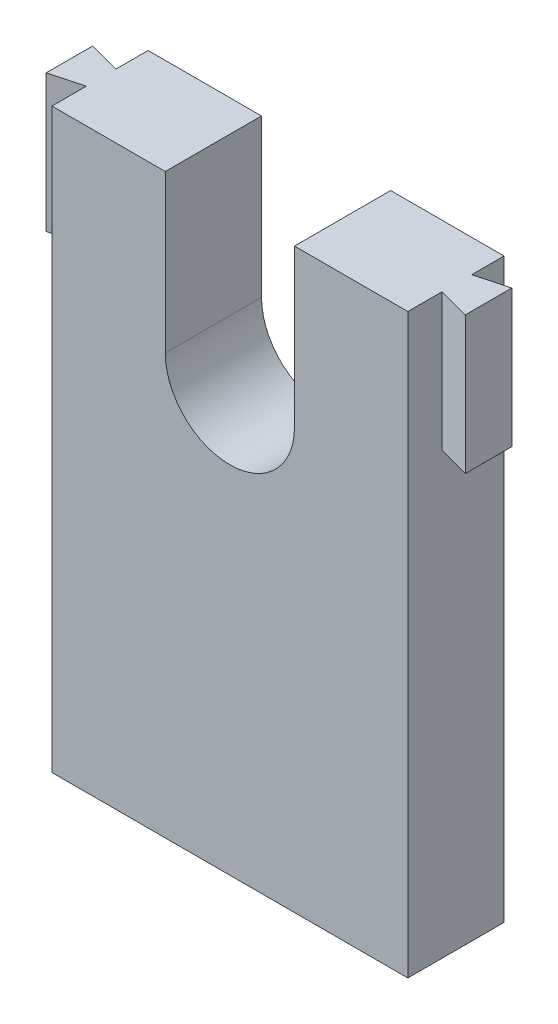
SolidWorks part; units mm, degrees
ref_plane "Front Plane" through (0, 0, 0) normal (0, 0, 1) x (1, 0, 0)
ref_plane "Top Plane" through (0, 0, 0) normal (0, 1, 0) x (1, 0, 0)
ref_plane "Right Plane" through (0, 0, 0) normal (1, 0, 0) x (0, 0, -1)
sketch "Sketch1" plane through (0, 0, 0) normal (0, 0, 1) x (1, 0, 0)
  line L1 (-13.8584, 22.099) -> (12.0416, 22.099)
  line L2 (-13.8584, 22.099) -> (-13.8584, -7.901)
  line L3 (-13.8584, -7.901) -> (12.0416, -7.901)
  line L4 (12.0416, 22.099) -> (12.0416, -7.901)
  dimension "D1" = 25.9
  dimension "D2" = 30
extrude "Boss-Extrude1" add sketch "Sketch1" along normal blind 7
sketch "Sketch2" plane through (0, 22.099, 0) normal (0, 1, 0) x (1, 0, 0)
  line L0 (-13.8584, -7) -> (-13.8584, -4.5) construction
  line L1 (-13.8584, -7) -> (-13.8584, 0) construction
  line L2 (-13.8584, -4.5) -> (-16.1584, -5.1163)
  line L3 (-16.1584, -5.1163) -> (-16.1584, -1.7337)
  line L4 (-16.1584, -1.7337) -> (-13.8584, -2.35)
  line L5 (-13.8584, -2.35) -> (-13.8584, 0) construction
  line L6 (12.0416, 0) -> (12.0416, -2.35) construction
  line L7 (12.0416, -7) -> (12.0416, 0) construction
  line L8 (12.0416, -2.35) -> (14.3416, -1.7337)
  line L9 (14.3416, -1.7337) -> (14.3416, -5.1163)
  line L10 (14.3416, -5.1163) -> (12.0416, -4.5)
  line L11 (12.0416, -4.5) -> (12.0416, -7) construction
  line L12 (12.0416, -2.35) -> (12.0416, -4.5)
  line L13 (-13.8584, -2.35) -> (-13.8584, -4.5)
  dimension "D1" = 2.3
  dimension "D2" = 105
  dimension "D3" = 105
  dimension "D4" = 2.15
  dimension "D5" = 2.35
  dimension "D6" = 2.35
  dimension "D7" = 2.15
  dimension "D8" = 105
  dimension "D9" = 105
  dimension "D11" = 2.3
extrude "Boss-Extrude2" add sketch "Sketch2" against normal blind 10
sketch "Sketch3" plane through (0, 0, 0) normal (0, 0, -1) x (-1, 0, 0)
  line L0 (-12.0416, 22.099) -> (13.8584, 22.099) construction
  line L2 (-3.7916, 10.6661) -> (-3.7916, 22.099)
  line L3 (5.6084, 10.6661) -> (5.6084, 22.099)
  line L4 (-3.7916, 22.099) -> (5.6084, 22.099)
  arc A0 (-3.7916, 10.6661) -> (5.6084, 10.6661) centre (0.9084, 10.6661) ccw
  dimension "D1" = 9.4
extrude "Cut-Extrude1" cut sketch "Sketch3" against normal blind 10
sketch "Sketch4" plane through (0, -7.901, 0) normal (0, -1, 0) x (1, 0, 0)
  line L1 (-13.8584, 7) -> (12.0416, 7)
  line L2 (-13.8584, 7) -> (-13.8584, 0)
  line L3 (-13.8584, 0) -> (12.0416, 0)
  line L4 (12.0416, 7) -> (12.0416, 0)
extrude "Boss-Extrude3" add sketch "Sketch4" along normal blind 12
